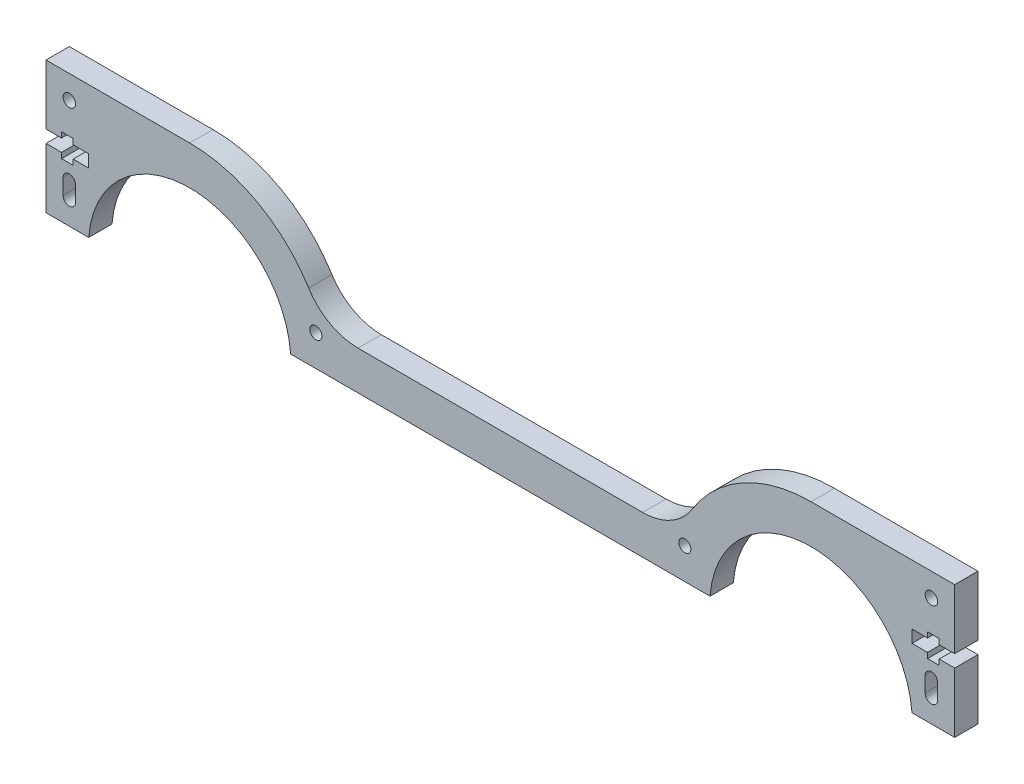
SolidWorks part; units mm, degrees
material "Balsa"
ref_plane "Plano frontal" through (0, 0, 0) normal (0, 0, 1) x (1, 0, 0)
ref_plane "Plano superior" through (0, 0, 0) normal (0, 1, 0) x (1, 0, 0)
ref_plane "Plano direito" through (0, 0, 0) normal (1, 0, 0) x (0, 0, -1)
sketch "Esboço1" plane through (0, 0, 0) normal (0, 0, 1) x (1, 0, 0)
  line L0 (-106, -30) -> (-117, -30)
  line L1 (54, -30) -> (0, -30)
  line L2 (-80, 4.0768) -> (-117, 4.0768)
  line L3 (-117, -11.3232) -> (-113, -11.3232)
  line L4 (-113, -11.3232) -> (-113, -9.9232)
  line L5 (-113, -9.9232) -> (-110, -9.9232)
  line L6 (-110, -9.9232) -> (-110, -11.3232)
  line L7 (-110, -11.3232) -> (-106, -11.3232)
  line L8 (-106, -11.3232) -> (-106, -14.5232)
  line L9 (-106, -14.5232) -> (-110, -14.5232)
  line L10 (-110, -14.5232) -> (-110, -15.9232)
  line L11 (-110, -15.9232) -> (-113, -15.9232)
  line L12 (-113, -15.9232) -> (-113, -14.5232)
  line L13 (-113, -14.5232) -> (-117, -14.5232)
  line L14 (117, -30) -> (106, -30)
  line L15 (0, 0) -> (0, -30) construction
  line L16 (-106, -12.9232) -> (-102.7088, -12.9232) construction
  line L17 (-36.6429, -20) -> (36.6429, -20)
  line L18 (-117, -14.5232) -> (-117, -30)
  line L19 (80, 4.0768) -> (117, 4.0768)
  line L32 (106, -12.9232) -> (102.7088, -12.9232) construction
  line L45 (113, -14.5232) -> (117, -14.5232)
  line L46 (113, -15.9232) -> (113, -14.5232)
  line L47 (110, -15.9232) -> (113, -15.9232)
  line L48 (110, -14.5232) -> (110, -15.9232)
  line L49 (106, -14.5232) -> (110, -14.5232)
  line L50 (106, -11.3232) -> (106, -14.5232)
  line L51 (110, -11.3232) -> (106, -11.3232)
  line L52 (110, -9.9232) -> (110, -11.3232)
  line L53 (113, -9.9232) -> (110, -9.9232)
  line L54 (113, -11.3232) -> (113, -9.9232)
  line L55 (117, -11.3232) -> (113, -11.3232)
  line L56 (117, -30) -> (117, -14.5232)
  line L58 (-117, 4.0768) -> (-117, -11.3232)
  line L59 (117, 4.0768) -> (117, -11.3232)
  line L60 (117, -14.5232) -> (117, -30)
  line L73 (0, -30) -> (-54, -30)
  arc A0 (-54, -30) -> (-106, -30) centre (-80, -32) ccw
  arc A1 (54, -30) -> (106, -30) centre (80, -32) cw
  arc A2 (-49.3758, -12.9292) -> (-80, 4.0768) centre (-80, -32) ccw
  arc A3 (49.3758, -12.9292) -> (80, 4.0768) centre (80, -32) cw
  circle A4 centre (-47.5, -22) radius 1.55
  circle A5 centre (47.5, -22) radius 1.55
  arc A6 (-36.6429, -20) -> (-49.3758, -12.9292) centre (-36.6429, -5) cw
  arc A7 (49.3758, -12.9292) -> (36.6429, -20) centre (36.6429, -5) cw
  point P28 (0, -20)
  point P41 (-45.9774, -20)
  point P44 (45.9774, -20)
  dimension "D6" = 52
  dimension "D11" = 160
  dimension "D10" = 10
  dimension "D15" = 3.1
  dimension "D17" = 15
  dimension "D1" = 4
  dimension "D2" = 3.2
  dimension "D3" = 3
  dimension "D4" = 6
  dimension "D5" = 234
  dimension "D7" = 2
  dimension "D8" = 4
  dimension "D9" = 10
  dimension "D12" = 17
  dimension "D13" = 30
  dimension "D14" = 8
  dimension "D16" = 95
extrude "Ressalto-extrusão1" add sketch "Esboço1" along normal blind 6
sketch "Esboço2" plane through (0, 0, 6) normal (0, 0, 1) x (1, 0, 0)
  line L0 (0, 0) -> (0, 26.3693) construction
  line L1 (-117, 4.0768) -> (-117, -11.3232) construction
  line L2 (-80, 4.0768) -> (-117, 4.0768) construction
  line L3 (-111, -19.9232) -> (-111, -23.9232) construction
  line L4 (-109.4, -19.9232) -> (-109.4, -23.9232)
  line L5 (-112.6, -19.9232) -> (-112.6, -23.9232)
  line L6 (111, -19.9232) -> (111, -23.9232) construction
  line L7 (109.4, -19.9232) -> (109.4, -23.9232)
  line L8 (112.6, -19.9232) -> (112.6, -23.9232)
  circle A0 centre (-111, -1.9232) radius 1.6
  circle A1 centre (111, -1.9232) radius 1.6
  arc A2 (-109.4, -19.9232) -> (-112.6, -19.9232) centre (-111, -19.9232) ccw
  arc A3 (-112.6, -23.9232) -> (-109.4, -23.9232) centre (-111, -23.9232) ccw
  arc A4 (109.4, -19.9232) -> (112.6, -19.9232) centre (111, -19.9232) cw
  arc A5 (112.6, -23.9232) -> (109.4, -23.9232) centre (111, -23.9232) cw
  point P13 (-111, -21.9232)
  point P21 (111, -21.9232)
  dimension "D3" = 3.2
  dimension "D1" = 6
  dimension "D2" = 6
  dimension "D4" = 20
  dimension "D5" = 4
extrude "Corte-extrusão1" cut sketch "Esboço2" against normal blind 10
